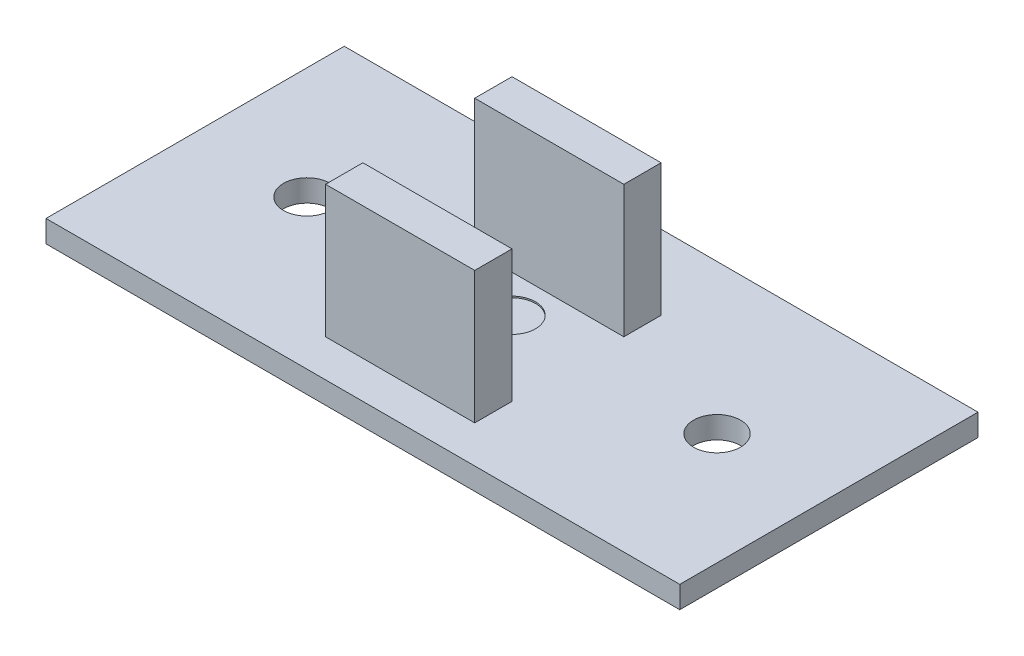
SolidWorks part; units mm, degrees
ref_plane "Front Plane" through (0, 0, 0) normal (0, 0, 1) x (1, 0, 0)
ref_plane "Top Plane" through (0, 0, 0) normal (0, 1, 0) x (1, 0, 0)
ref_plane "Right Plane" through (0, 0, 0) normal (1, 0, 0) x (0, 0, -1)
sketch "Sketch1" plane through (0, 0, 0) normal (0, 1, 0) x (1, 0, 0)
  line L0 (0, 10.16) -> (43.18, 10.16) construction
  line L1 (0, 0) -> (43.18, 0)
  line L2 (0, 0) -> (0, 20.32)
  line L3 (0, 20.32) -> (43.18, 20.32)
  line L4 (43.18, 0) -> (43.18, 20.32)
  line L5 (21.59, 20.32) -> (21.59, 0) construction
  circle A0 centre (7.62, 10.16) radius 1.6
  circle A1 centre (35.56, 10.16) radius 1.6
  dimension "D4" = 3.2
  dimension "D1" = 43.18
  dimension "D2" = 20.32
  dimension "D3" = 7.62
extrude "Boss-Extrude1" add sketch "Sketch1" along normal blind 1.5
sketch "Sketch2" plane through (0, 1.5, 0) normal (0, 1, 0) x (1, 0, 0)
  line L0 (0, 0) -> (43.18, 0) construction
  line L1 (16.51, 5.08) -> (26.67, 5.08)
  line L2 (16.51, 5.08) -> (16.51, 2.54)
  line L3 (16.51, 2.54) -> (26.67, 2.54)
  line L4 (26.67, 5.08) -> (26.67, 2.54)
  line L5 (16.51, 15.24) -> (16.51, 12.7)
  line L6 (16.51, 15.24) -> (26.67, 15.24)
  line L7 (26.67, 15.24) -> (26.67, 12.7)
  line L8 (16.51, 12.7) -> (26.67, 12.7)
  point P6 (21.59, 0)
  point P7 (21.59, 2.54)
  point P8 (16.51, 3.81)
  point P9 (16.51, 13.97)
  dimension "D1" = 2.54
  dimension "D2" = 2.54
  dimension "D3" = 10.16
  dimension "D5" = 10.16
  dimension "D4" = 2
extrude "Boss-Extrude2" add sketch "Sketch2" along normal blind 9 separate body
ref_plane "Plane1" through (0, 0, -3.81) normal (0, 0, -1) x (-1, 0, 0)
ref_plane "Plane2" through (21.59, 0, 0) normal (1, 0, 0) x (0, 0, -1)
sketch "Sketch5" plane through (0, 1.5, 0) normal (0, 1, 0) x (1, 0, 0)
  line L0 (35.56, 10.16) -> (7.62, 10.16) construction
  circle A0 centre (35.56, 10.16) radius 1.6 construction
  circle A1 centre (7.62, 10.16) radius 1.6 construction
  circle A2 centre (21.59, 10.16) radius 1.6
extrude "Cut-Extrude1" cut sketch "Sketch5" against normal blind 0.1
equation "\"D1@Sketch1\"=17*2.54"
equation "\"D2@Sketch1\"=8*2.54"
equation "\"D3@Sketch1\"=3*2.54"
